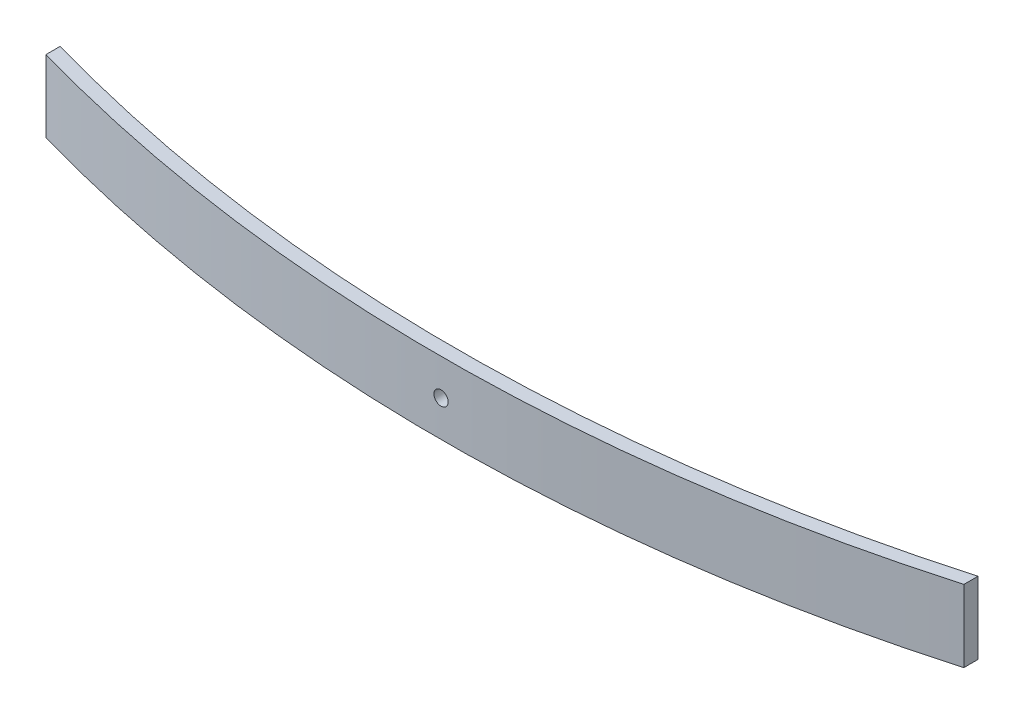
SolidWorks part; units mm, degrees
ref_plane "Front Plane" through (0, 0, 0) normal (0, 0, 1) x (1, 0, 0)
ref_plane "Top Plane" through (0, 0, 0) normal (0, 1, 0) x (1, 0, 0)
ref_plane "Right Plane" through (0, 0, 0) normal (1, 0, 0) x (0, 0, -1)
sketch "Sketch1" plane through (0, 0, 0) normal (0, 1, 0) x (1, 0, 0)
  line L0 (-630, 0) -> (630, 0) construction
  line L1 (-210.8013, -133) -> (245.5549, -133) construction
  line L2 (0, 0) -> (0, -133) construction
  line L3 (-602.5798, 17.4465) -> (-589.9243, 25.4988)
  line L4 (-616.835, -11.5296) -> (-605.5506, -21.4121)
  line L5 (616.835, -11.5296) -> (605.5506, -21.4121)
  line L6 (-630.0217, -47.5) -> (-630.0217, -62.5)
  line L7 (602.5798, 17.4465) -> (589.9243, 25.4988)
  line L8 (630.0217, -47.5) -> (630.0217, -62.5)
  line L9 (-545.0217, -92.3065) -> (-545.0217, -107.3065)
  line L10 (545.0217, -92.3065) -> (545.0217, -107.3065)
  line L11 (-485.0217, -125.4896) -> (-485.0217, -140.4896)
  line L12 (485.0217, -125.4896) -> (485.0217, -140.4896)
  arc A0 (-616.835, -11.5296) -> (-630, -17.5) centre (-630, 0) ccw
  arc A1 (630, -17.5) -> (616.835, -11.5296) centre (630, 0) ccw
  arc A2 (-630, -17.5) -> (630, -17.5) centre (0, 1642.9318) ccw
  arc A3 (-630.0011, -32.5) -> (630.0011, -32.5) centre (0, 1627.9379) ccw
  arc A4 (-605.5506, -21.4121) -> (-630.0011, -32.5) centre (-630, 0) ccw
  arc A5 (630.0011, -32.5) -> (605.5506, -21.4121) centre (630, 0) ccw
  arc A6 (-630.0217, -47.5) -> (630.0217, -47.5) centre (0, 1613.05) ccw
  arc A7 (630.0217, -47.5) -> (589.9243, 25.4988) centre (630, 0) ccw
  arc A8 (-589.9243, 25.4988) -> (-630.0217, -47.5) centre (-630, 0) ccw
  arc A9 (-630.0217, -62.5) -> (630.0217, -62.5) centre (0, 1598.05) ccw
  arc A10 (545.0217, -107.3065) -> (-545.0217, -107.3065) centre (0, 1583.05) cw
  arc A11 (485.0217, -140.4896) -> (-485.0217, -140.4896) centre (0, 1568.05) cw
  point P5 (-630.0217, -47.5)
  point P6 (0, -163)
  point P10 (0, -133)
  point P13 (-630.0011, -32.5)
  point P14 (0, -148)
  point P15 (630.0011, -32.5)
  point P20 (630.0217, -47.5)
  point P27 (0, -178)
  point P37 (0, -193)
  point P40 (630.0217, -55)
  point P44 (0, -208)
  dimension "D4" = 35
  dimension "D5" = 35
  dimension "D9" = 15
  dimension "D12" = 15
  dimension "D1" = 133
  dimension "D2" = 630
  dimension "D3" = 630
  dimension "D6" = 15
  dimension "D7" = 15
  dimension "D8" = 15
  dimension "D10" = 15
  dimension "D11" = 15
  dimension "D13" = 15
  dimension "D14" = 15
  dimension "D15" = 15
  dimension "D16" = 85
  dimension "D17" = 15
  dimension "D18" = 15
  dimension "D19" = 85
  dimension "D20" = 60
  dimension "D21" = 15
  dimension "D22" = 15
  dimension "D23" = 15
  dimension "D24" = 60
sketch "Sketch5" plane through (0, 0, 0) normal (0, 0, 1) x (1, 0, 0)
  circle A0 centre (0, 38.1) radius 7.5
  dimension "D2" = 15
  dimension "D1" = 38.1
sketch "Sketch6" plane through (0, 0, 0) normal (0, 0, 1) x (1, 0, 0)
  circle A0 centre (0, 38.1) radius 7.5
sketch "Sketch7" plane through (0, 0, 0) normal (0, 0, 1) x (1, 0, 0)
  circle A0 centre (0, 38.1) radius 7.5
sketch "Sketch8" plane through (0, 0, 0) normal (0, 0, 1) x (1, 0, 0)
  circle A0 centre (0, 38.1) radius 7.5
extrude "Boss-Extrude1" add sketch "Sketch1" along normal blind 76.2 contours A11 L12 A10 L11
sketch "Sketch9" plane through (0, 0, 0) normal (0, 0, 1) x (1, 0, 0)
  circle A0 centre (0, 38.1) radius 7.5
extrude "Cut-Extrude1" cut sketch "Sketch9" along normal through all
